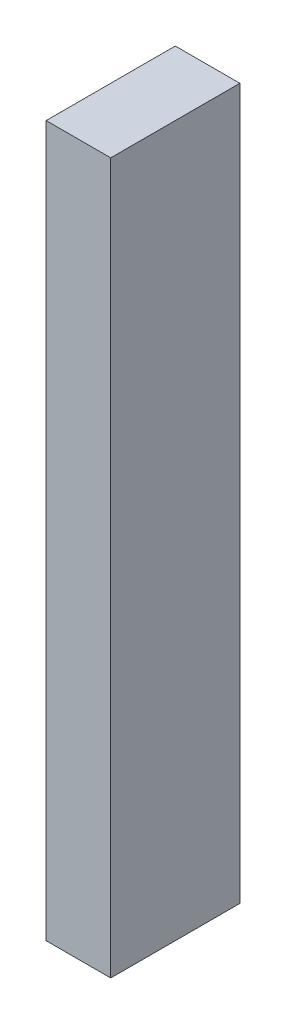
SolidWorks part; units mm, degrees
ref_plane "Front Plane" through (0, 0, 0) normal (0, 0, 1) x (1, 0, 0)
ref_plane "Top Plane" through (0, 0, 0) normal (0, 1, 0) x (1, 0, 0)
ref_plane "Right Plane" through (0, 0, 0) normal (1, 0, 0) x (0, 0, -1)
sketch "Sketch1" plane through (0, 0, 0) normal (0, 1, 0) x (1, 0, 0)
  line L1 (0, 0) -> (25.4, 0)
  line L2 (0, 0) -> (0, 50.8)
  line L3 (0, 50.8) -> (25.4, 50.8)
  line L4 (25.4, 0) -> (25.4, 50.8)
  dimension "D1" = 25.4
  dimension "D2" = 50.8
extrude "Boss-Extrude1" add sketch "Sketch1" along normal blind 279.4
